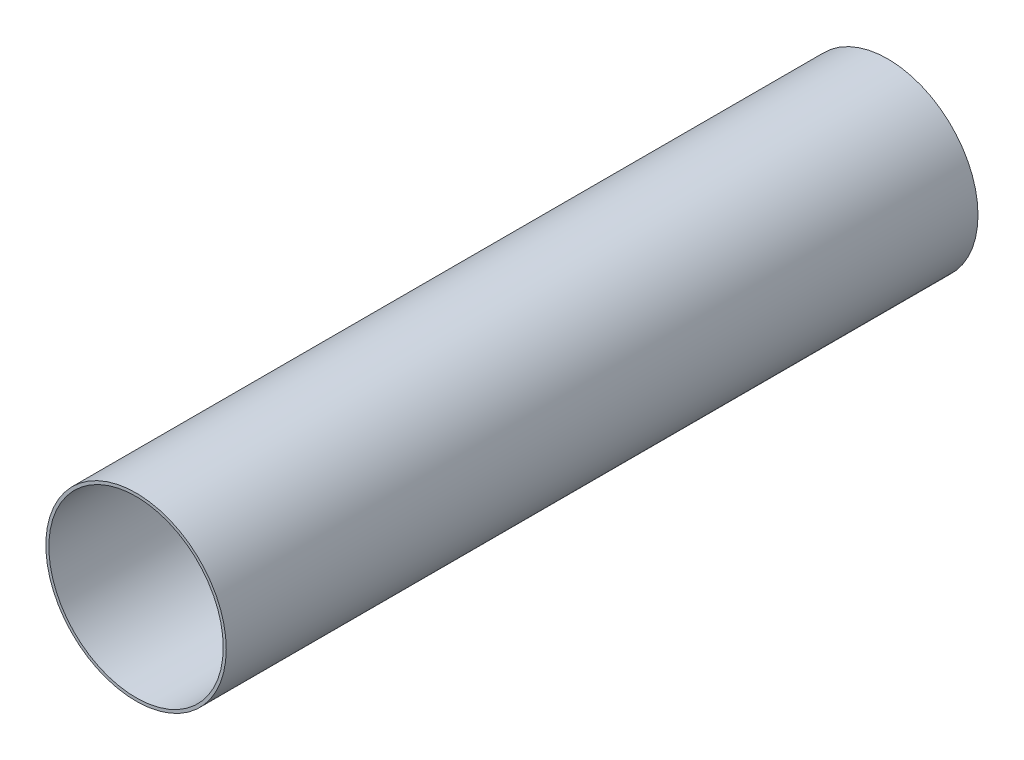
SolidWorks part; units mm, degrees
ref_plane "Plan de face" through (0, 0, 0) normal (0, 0, 1) x (1, 0, 0)
ref_plane "Plan de dessus" through (0, 0, 0) normal (0, 1, 0) x (1, 0, 0)
ref_plane "Plan de droite" through (0, 0, 0) normal (1, 0, 0) x (0, 0, -1)
sketch "Esquisse1" plane through (0, 0, 0) normal (0, 0, 1) x (1, 0, 0)
  circle A0 centre (0, 0) radius 30
  circle A1 centre (0, 0) radius 29
extrude "Boss.-Extru.1" add sketch "Esquisse1" along normal blind 250
